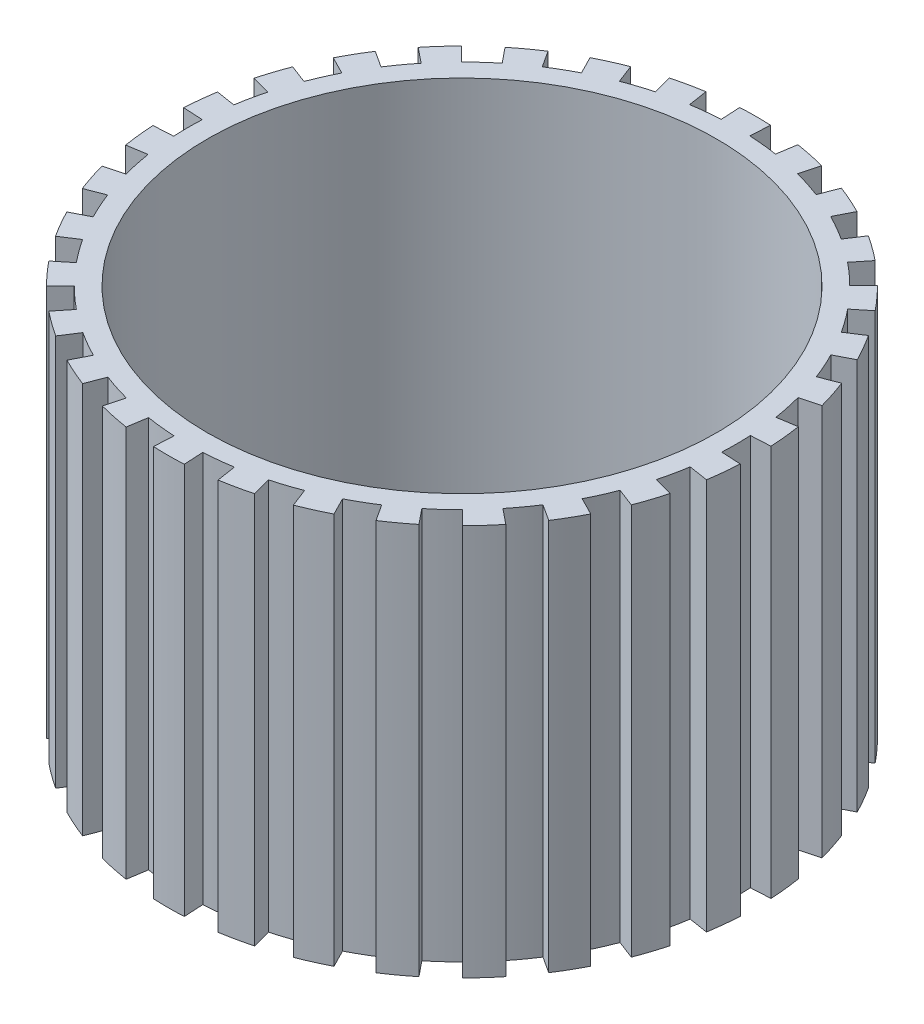
SolidWorks part; units mm, degrees
material "Rubber"
ref_plane "Front Plane" through (0, 0, 0) normal (0, 0, 1) x (1, 0, 0)
ref_plane "Top Plane" through (0, 0, 0) normal (0, 1, 0) x (1, 0, 0)
ref_plane "Right Plane" through (0, 0, 0) normal (1, 0, 0) x (0, 0, -1)
sketch "Sketch2" plane through (0, 0, 0) normal (0, 1, 0) x (1, 0, 0)
  line L0 (-11.0126, 69.1283) -> (-11.7992, 74.066)
  line L2 (-3.7264, 69.9007) -> (-3.9926, 74.8937)
  line L3 (3.6006, 69.9073) -> (3.8578, 74.9007)
  line L4 (10.8882, 69.148) -> (11.6659, 74.0871)
  line L5 (18.0565, 67.6311) -> (19.3463, 72.4619)
  line L6 (25.027, 65.3732) -> (26.8146, 70.0427)
  line L7 (31.7232, 62.399) -> (33.9892, 66.8561)
  line L8 (38.0719, 58.7412) -> (40.7913, 62.937)
  line L9 (44.0035, 54.4398) -> (47.1466, 58.3284)
  line L10 (49.4529, 49.542) -> (52.9853, 53.0807)
  line L11 (54.3606, 44.1013) -> (58.2435, 47.2514)
  line L12 (58.6726, 38.1775) -> (62.8635, 40.9045)
  line L13 (62.3418, 31.8354) -> (66.7948, 34.1094)
  line L14 (65.328, 25.1445) -> (69.9943, 26.9406)
  line L15 (67.5985, 18.1781) -> (72.4269, 19.4766)
  line L16 (69.1283, 11.0126) -> (74.066, 11.7992)
  line L17 (69.9007, 3.7264) -> (74.8937, 3.9926)
  line L18 (69.9073, -3.6006) -> (74.9007, -3.8578)
  line L19 (69.148, -10.8882) -> (74.0871, -11.6659)
  line L20 (67.6311, -18.0565) -> (72.4619, -19.3463)
  line L21 (65.3732, -25.027) -> (70.0427, -26.8146)
  line L22 (62.399, -31.7232) -> (66.8561, -33.9892)
  line L23 (58.7412, -38.0719) -> (62.937, -40.7913)
  line L24 (54.4398, -44.0035) -> (58.3284, -47.1466)
  line L25 (49.542, -49.4529) -> (53.0807, -52.9853)
  line L26 (44.1013, -54.3606) -> (47.2514, -58.2435)
  line L27 (38.1775, -58.6726) -> (40.9045, -62.8635)
  line L28 (31.8354, -62.3418) -> (34.1094, -66.7948)
  line L29 (25.1445, -65.328) -> (26.9406, -69.9943)
  line L30 (18.1781, -67.5985) -> (19.4766, -72.4269)
  line L31 (11.0126, -69.1283) -> (11.7992, -74.066)
  line L32 (3.7264, -69.9007) -> (3.9926, -74.8937)
  line L33 (-3.6006, -69.9073) -> (-3.8578, -74.9007)
  line L34 (-10.8882, -69.148) -> (-11.6659, -74.0871)
  line L35 (-18.0565, -67.6311) -> (-19.3463, -72.4619)
  line L36 (-25.027, -65.3732) -> (-26.8146, -70.0427)
  line L37 (-31.7232, -62.399) -> (-33.9892, -66.8561)
  line L38 (-38.0719, -58.7412) -> (-40.7913, -62.937)
  line L39 (-44.0035, -54.4398) -> (-47.1466, -58.3284)
  line L40 (-49.4529, -49.542) -> (-52.9853, -53.0807)
  line L41 (-54.3606, -44.1013) -> (-58.2435, -47.2514)
  line L42 (-58.6726, -38.1775) -> (-62.8635, -40.9045)
  line L43 (-62.3418, -31.8354) -> (-66.7948, -34.1094)
  line L44 (-65.328, -25.1445) -> (-69.9943, -26.9406)
  line L45 (-67.5985, -18.1781) -> (-72.4269, -19.4766)
  line L46 (-69.1283, -11.0126) -> (-74.066, -11.7992)
  line L47 (-69.9007, -3.7264) -> (-74.8937, -3.9926)
  line L48 (-69.9073, 3.6006) -> (-74.9007, 3.8578)
  line L49 (-69.148, 10.8882) -> (-74.0871, 11.6659)
  line L50 (-67.6311, 18.0565) -> (-72.4619, 19.3463)
  line L51 (-65.3732, 25.027) -> (-70.0427, 26.8146)
  line L52 (-62.399, 31.7232) -> (-66.8561, 33.9892)
  line L53 (-58.7412, 38.0719) -> (-62.937, 40.7913)
  line L54 (-54.4398, 44.0035) -> (-58.3284, 47.1466)
  line L55 (-49.542, 49.4529) -> (-53.0807, 52.9853)
  line L56 (-44.1013, 54.3606) -> (-47.2514, 58.2435)
  line L57 (-38.1775, 58.6726) -> (-40.9045, 62.8635)
  line L59 (-18.1781, 67.5985) -> (-19.4766, 72.4269)
  line L60 (0, 0) -> (-16.8797, 62.77) construction
  line L61 (0, 0) -> (-10.226, 64.1906) construction
  line L62 (-16.8797, 62.77) -> (-18.1781, 67.5985) construction
  line L63 (-10.226, 64.1906) -> (-11.0126, 69.1283) construction
  line L64 (0, 0) -> (-4.6068, 86.4158) [skipped]
  line L65 (0, 0) -> (4.4513, 86.4239) [skipped]
  line L66 (0, 0) -> (13.4607, 85.4852) [skipped]
  line L67 (0, 0) -> (22.3226, 83.6098) [skipped]
  line L68 (0, 0) -> (30.9399, 80.8185) [skipped]
  line L69 (0, 0) -> (39.2183, 77.1416) [skipped]
  line L70 (0, 0) -> (47.0669, 72.6196) [skipped]
  line L71 (0, 0) -> (54.3999, 67.302) [skipped]
  line L72 (0, 0) -> (61.1369, 61.247) [skipped]
  line L73 (0, 0) -> (67.204, 54.5209) [skipped]
  line L74 (0, 0) -> (72.5348, 47.1975) [skipped]
  line L75 (0, 0) -> (77.071, 39.357) [skipped]
  line L76 (0, 0) -> (80.7627, 31.0853) [skipped]
  line L77 (0, 0) -> (83.5696, 22.473) [skipped]
  line L78 (0, 0) -> (85.4608, 13.6145) [skipped]
  line L79 (0, 0) -> (86.4158, 4.6068) [skipped]
  line L80 (0, 0) -> (86.4239, -4.4513) [skipped]
  line L81 (0, 0) -> (85.4852, -13.4607) [skipped]
  line L82 (0, 0) -> (83.6098, -22.3226) [skipped]
  line L83 (0, 0) -> (80.8185, -30.9399) [skipped]
  line L84 (0, 0) -> (77.1416, -39.2183) [skipped]
  line L85 (0, 0) -> (72.6196, -47.0669) [skipped]
  line L86 (0, 0) -> (67.302, -54.3999) [skipped]
  line L87 (0, 0) -> (61.247, -61.1369) [skipped]
  line L88 (0, 0) -> (54.5209, -67.204) [skipped]
  line L89 (0, 0) -> (47.1975, -72.5348) [skipped]
  line L90 (0, 0) -> (39.357, -77.071) [skipped]
  line L91 (0, 0) -> (31.0853, -80.7627) [skipped]
  line L92 (0, 0) -> (22.473, -83.5696) [skipped]
  line L93 (0, 0) -> (13.6145, -85.4608) [skipped]
  line L94 (0, 0) -> (4.6068, -86.4158) [skipped]
  line L95 (0, 0) -> (-4.4513, -86.4239) [skipped]
  line L96 (0, 0) -> (-13.4607, -85.4852) [skipped]
  line L97 (0, 0) -> (-22.3226, -83.6098) [skipped]
  line L98 (0, 0) -> (-30.9399, -80.8185) [skipped]
  line L99 (0, 0) -> (-39.2183, -77.1416) [skipped]
  line L100 (0, 0) -> (-47.0669, -72.6196) [skipped]
  line L101 (0, 0) -> (-54.3999, -67.302) [skipped]
  line L102 (0, 0) -> (-61.1369, -61.247) [skipped]
  line L103 (0, 0) -> (-67.204, -54.5209) [skipped]
  line L104 (0, 0) -> (-72.5348, -47.1975) [skipped]
  line L105 (0, 0) -> (-77.071, -39.357) [skipped]
  line L106 (0, 0) -> (-80.7627, -31.0853) [skipped]
  line L107 (0, 0) -> (-83.5696, -22.473) [skipped]
  line L108 (0, 0) -> (-85.4608, -13.6145) [skipped]
  line L109 (0, 0) -> (-86.4158, -4.6068) [skipped]
  line L110 (0, 0) -> (-86.4239, 4.4513) [skipped]
  line L111 (0, 0) -> (-85.4852, 13.4607) [skipped]
  line L112 (0, 0) -> (-83.6098, 22.3226) [skipped]
  line L113 (0, 0) -> (-80.8185, 30.9399) [skipped]
  line L114 (0, 0) -> (-77.1416, 39.2183) [skipped]
  line L115 (0, 0) -> (-72.6196, 47.0669) [skipped]
  line L116 (0, 0) -> (-67.302, 54.3999) [skipped]
  line L117 (0, 0) -> (-61.247, 61.1369) [skipped]
  line L118 (0, 0) -> (-54.5209, 67.204) [skipped]
  line L119 (0, 0) -> (-47.1975, 72.5348) [skipped]
  line L120 (0, 0) -> (-31.0853, 80.7627) [skipped]
  line L121 (0, 0) -> (-39.357, 77.071) [skipped]
  line L122 (-31.8354, 62.3418) -> (-34.1094, 66.7948)
  line L123 (-25.1445, 65.328) -> (-26.9406, 69.9943)
  arc A0 (-11.7992, 74.066) -> (-19.4766, 72.4269) centre (0, 0) ccw
  arc A1 (-44.1013, 54.3606) -> (-49.542, 49.4529) centre (0, 0) ccw
  circle A2 centre (0, 0) radius 65
  arc A3 (3.8578, 74.9007) -> (-3.9926, 74.8937) centre (0, 0) ccw
  arc A5 (19.3463, 72.4619) -> (11.6659, 74.0871) centre (0, 0) ccw
  arc A6 (33.9892, 66.8561) -> (26.8146, 70.0427) centre (0, 0) ccw
  arc A7 (47.1466, 58.3284) -> (40.7913, 62.937) centre (0, 0) ccw
  arc A8 (58.2435, 47.2514) -> (52.9853, 53.0807) centre (0, 0) ccw
  arc A9 (66.7948, 34.1094) -> (62.8635, 40.9045) centre (0, 0) ccw
  arc A10 (72.4269, 19.4766) -> (69.9943, 26.9406) centre (0, 0) ccw
  arc A11 (74.8937, 3.9926) -> (74.066, 11.7992) centre (0, 0) ccw
  arc A12 (74.0871, -11.6659) -> (74.9007, -3.8578) centre (0, 0) ccw
  arc A13 (70.0427, -26.8146) -> (72.4619, -19.3463) centre (0, 0) ccw
  arc A14 (62.937, -40.7913) -> (66.8561, -33.9892) centre (0, 0) ccw
  arc A15 (53.0807, -52.9853) -> (58.3284, -47.1466) centre (0, 0) ccw
  arc A16 (40.9045, -62.8635) -> (47.2514, -58.2435) centre (0, 0) ccw
  arc A17 (26.9406, -69.9943) -> (34.1094, -66.7948) centre (0, 0) ccw
  arc A18 (11.7992, -74.066) -> (19.4766, -72.4269) centre (0, 0) ccw
  arc A19 (-3.8578, -74.9007) -> (3.9926, -74.8937) centre (0, 0) ccw
  arc A20 (-19.3463, -72.4619) -> (-11.6659, -74.0871) centre (0, 0) ccw
  arc A21 (-33.9892, -66.8561) -> (-26.8146, -70.0427) centre (0, 0) ccw
  arc A22 (-47.1466, -58.3284) -> (-40.7913, -62.937) centre (0, 0) ccw
  arc A23 (-58.2435, -47.2514) -> (-52.9853, -53.0807) centre (0, 0) ccw
  arc A24 (-66.7948, -34.1094) -> (-62.8635, -40.9045) centre (0, 0) ccw
  arc A25 (-72.4269, -19.4766) -> (-69.9943, -26.9406) centre (0, 0) ccw
  arc A26 (-74.8937, -3.9926) -> (-74.066, -11.7992) centre (0, 0) ccw
  arc A27 (-74.0871, 11.6659) -> (-74.9007, 3.8578) centre (0, 0) ccw
  arc A28 (-70.0427, 26.8146) -> (-72.4619, 19.3463) centre (0, 0) ccw
  arc A29 (-62.937, 40.7913) -> (-66.8561, 33.9892) centre (0, 0) ccw
  arc A30 (-53.0807, 52.9853) -> (-58.3284, 47.1466) centre (0, 0) ccw
  arc A31 (-40.9045, 62.8635) -> (-47.2514, 58.2435) centre (0, 0) ccw
  arc A32 (-26.9406, 69.9943) -> (-34.1094, 66.7948) centre (0, 0) ccw
  arc A33 (-38.1775, 58.6726) -> (-44.1013, 54.3606) centre (0, 0) ccw construction
  arc A34 (-31.8354, 62.3418) -> (-38.1775, 58.6726) centre (0, 0) ccw
  arc A35 (-25.1445, 65.328) -> (-31.8354, 62.3418) centre (0, 0) ccw construction
  arc A36 (-54.4398, 44.0035) -> (-58.7412, 38.0719) centre (0, 0) ccw
  arc A37 (-49.542, 49.4529) -> (-54.4398, 44.0035) centre (0, 0) ccw construction
  arc A38 (-62.399, 31.7232) -> (-65.3732, 25.027) centre (0, 0) ccw
  arc A39 (-58.7412, 38.0719) -> (-62.399, 31.7232) centre (0, 0) ccw construction
  arc A40 (-67.6311, 18.0565) -> (-69.148, 10.8882) centre (0, 0) ccw
  arc A41 (-65.3732, 25.027) -> (-67.6311, 18.0565) centre (0, 0) ccw construction
  arc A42 (-69.9073, 3.6006) -> (-69.9007, -3.7264) centre (0, 0) ccw
  arc A43 (-69.148, 10.8882) -> (-69.9073, 3.6006) centre (0, 0) ccw construction
  arc A44 (-69.1283, -11.0126) -> (-67.5985, -18.1781) centre (0, 0) ccw
  arc A45 (-69.9007, -3.7264) -> (-69.1283, -11.0126) centre (0, 0) ccw construction
  arc A46 (-65.328, -25.1445) -> (-62.3418, -31.8354) centre (0, 0) ccw
  arc A47 (-67.5985, -18.1781) -> (-65.328, -25.1445) centre (0, 0) ccw construction
  arc A48 (-58.6726, -38.1775) -> (-54.3606, -44.1013) centre (0, 0) ccw
  arc A49 (-62.3418, -31.8354) -> (-58.6726, -38.1775) centre (0, 0) ccw construction
  arc A50 (-49.4529, -49.542) -> (-44.0035, -54.4398) centre (0, 0) ccw
  arc A51 (-54.3606, -44.1013) -> (-49.4529, -49.542) centre (0, 0) ccw construction
  arc A52 (-38.0719, -58.7412) -> (-31.7232, -62.399) centre (0, 0) ccw
  arc A53 (-44.0035, -54.4398) -> (-38.0719, -58.7412) centre (0, 0) ccw construction
  arc A54 (-25.027, -65.3732) -> (-18.0565, -67.6311) centre (0, 0) ccw
  arc A55 (-10.8882, -69.148) -> (-3.6006, -69.9073) centre (0, 0) ccw
  arc A56 (3.7264, -69.9007) -> (11.0126, -69.1283) centre (0, 0) ccw
  arc A57 (18.1781, -67.5985) -> (25.1445, -65.328) centre (0, 0) ccw
  arc A58 (31.8354, -62.3418) -> (38.1775, -58.6726) centre (0, 0) ccw
  arc A59 (44.1013, -54.3606) -> (49.542, -49.4529) centre (0, 0) ccw
  arc A60 (54.4398, -44.0035) -> (58.7412, -38.0719) centre (0, 0) ccw
  arc A61 (62.399, -31.7232) -> (65.3732, -25.027) centre (0, 0) ccw
  arc A62 (67.6311, -18.0565) -> (69.148, -10.8882) centre (0, 0) ccw
  arc A63 (69.9073, -3.6006) -> (69.9007, 3.7264) centre (0, 0) ccw
  arc A64 (69.1283, 11.0126) -> (67.5985, 18.1781) centre (0, 0) ccw
  arc A65 (65.328, 25.1445) -> (62.3418, 31.8354) centre (0, 0) ccw
  arc A66 (58.6726, 38.1775) -> (54.3606, 44.1013) centre (0, 0) ccw
  arc A67 (49.4529, 49.542) -> (44.0035, 54.4398) centre (0, 0) ccw
  arc A68 (38.0719, 58.7412) -> (31.7232, 62.399) centre (0, 0) ccw
  arc A69 (-18.1781, 67.5985) -> (-25.1445, 65.328) centre (0, 0) ccw
  arc A70 (-3.7264, 69.9007) -> (-11.0126, 69.1283) centre (0, 0) ccw
  arc A71 (10.8882, 69.148) -> (3.6006, 69.9073) centre (0, 0) ccw
  arc A72 (25.027, 65.3732) -> (18.0565, 67.6311) centre (0, 0) ccw
  point P3 (-74.5821, -7.9067)
  dimension "D1" = 60
  dimension "D3" = 130
  dimension "D4" = 70
  dimension "D5" = 75
  dimension "D2" = 30
extrude "Boss-Extrude1" add sketch "Sketch2" along normal blind 100
